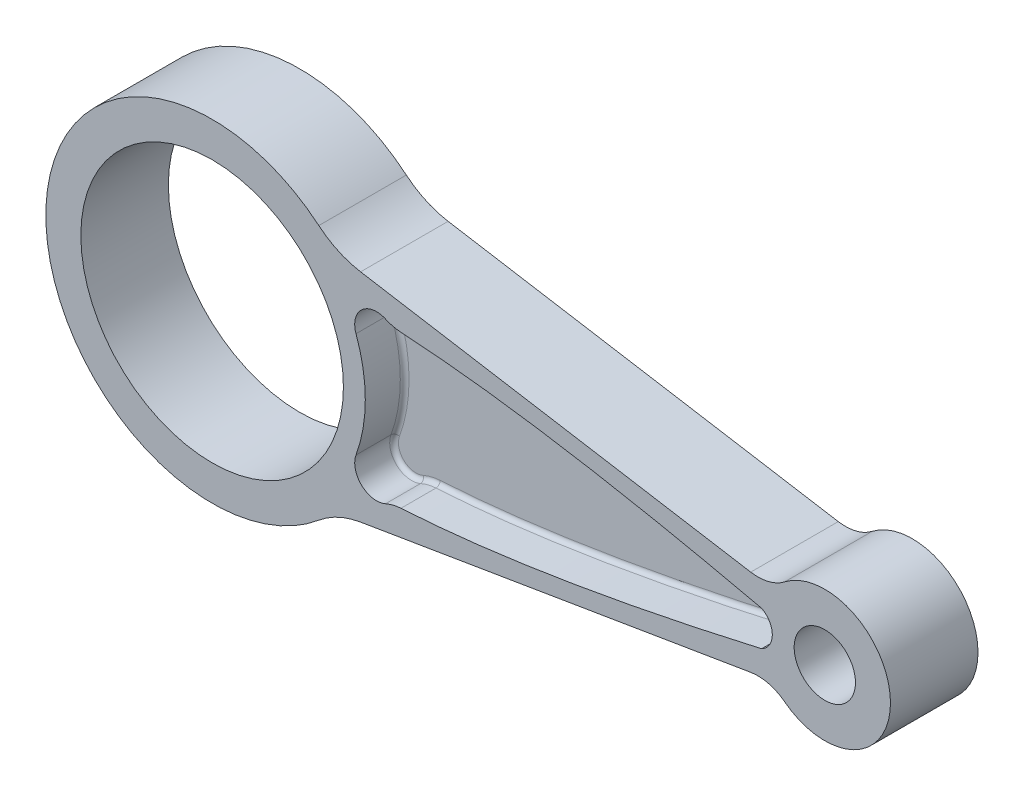
SolidWorks part; units mm, degrees
material "Plain Carbon Steel"
ref_plane "Front Plane" through (0, 0, 0) normal (0, 0, 1) x (1, 0, 0)
ref_plane "Top Plane" through (0, 0, 0) normal (0, 1, 0) x (1, 0, 0)
ref_plane "Right Plane" through (0, 0, 0) normal (1, 0, 0) x (0, 0, -1)
sketch "Sketch1" plane through (0, 0, 0) normal (0, 0, 1) x (1, 0, 0)
  line L0 (27.9355, 25.7606) -> (128.0638, 9.0844)
  line L1 (27.9355, -25.7606) -> (128.0638, -9.0844)
  line L2 (0, 0) -> (140, 0) construction
  circle A0 centre (0, 0) radius 30
  circle A1 centre (140, 0) radius 7
  arc A2 (27.9355, 25.7606) -> (27.9355, -25.7606) centre (0, 0) ccw
  arc A3 (128.0638, -9.0844) -> (128.0638, 9.0844) centre (140, 0) ccw
  dimension "D1" = 60
  dimension "D2" = 14
  dimension "D4" = 76
  dimension "D5" = 30
  dimension "D3" = 140
extrude "Boss-Extrude1" add sketch "Sketch1" along normal mid plane 20
fillet "Fillet1" radius 20 2 edges at (27.9355, -25.7606, 0) (27.9355, 25.7606, 0)
fillet "Fillet2" radius 10 2 edges at (128.0638, -9.0844, 0) (128.0638, 9.0844, 0)
sketch "Sketch2" plane through (0, 0, -10) normal (0, 0, -1) x (-1, 0, 0)
  line L0 (0, 0) -> (-176.748, 0) construction
  line L3 (-40.8003, 17.5353) -> (-73.6972, 15.9327) construction
  line L4 (-40.8003, -17.5353) -> (-73.6972, -15.9327) construction
  line L5 (-73.6972, 15.9327) -> (-125.5616, 4) construction
  line L6 (-73.6972, -15.9327) -> (-125.5616, -4) construction
  line L9 (-33.9231, -24.7634) -> (-123.0688, -9.9163) construction
  arc A0 (-32.8786, -12) -> (-32.8786, 12) centre (0, 0) cw
  arc A1 (-125.5616, -4) -> (-125.5616, 4) centre (-123.5, 0) cw
  circle A2 centre (-140, 0) radius 7 construction
  circle A3 centre (0, 0) radius 30 construction
  arc A6 (-32.8786, 12) -> (-40.8003, 17.5353) centre (-37.5755, 13.7143) ccw
  arc A7 (-32.8786, -12) -> (-40.8003, -17.5353) centre (-37.5755, -13.7143) cw
  spline S0 degree 2 poles (-40.8003, -17.5353) (-73.6972, -15.9327) (-125.5616, -4) knots 0 0 0 1 1 1
  spline S1 degree 2 poles (-40.8003, 17.5353) (-73.6972, 15.9327) (-125.5616, 4) knots 0 0 0 1 1 1
  point P8 (-128, 0)
  point P10 (-133, 0)
  point P11 (-35, 0)
  point P14 (-30, 0)
  point P25 (-73.6972, 0)
  point P28 (-73.6972, -14.084)
  dimension "D1" = 4.5
  dimension "D2" = 5
  dimension "D4" = 4
  dimension "D5" = 12
  dimension "D3" = 5
  dimension "D6" = 6
  dimension "D7" = 5
  dimension "D8" = 8
extrude "Cut-Extrude1" cut sketch "Sketch2" against normal offset from surface (9 mm away) 1 from surface at 0 up to plane "Front Plane" starting at face at (73.2512, 0, -10)
mirror "Mirror1" about plane through (0, 0, 0) normal (0, 0, 1) of "Cut-Extrude1"
fillet "Fillet3" radius 10 4 edges at (40.8003, 17.5353, -5.5) (40.8003, -17.5353, -5.5) (40.8003, 17.5353, 5.5) (40.8003, -17.5353, 5.5)
fillet "Fillet4" radius 1 14 edges at (41.3486, 17.6806, -1) (34.1715, 17.3766, -1) (35, 0, -1) (34.1715, -17.3766, -1) (41.3486, -17.6806, -1) (41.3486, 17.6806, 1) (34.1715, 17.3766, 1) (35, 0, 1) (34.1715, -17.3766, 1) (41.3486, -17.6806, 1)
split line "Split Line1"
